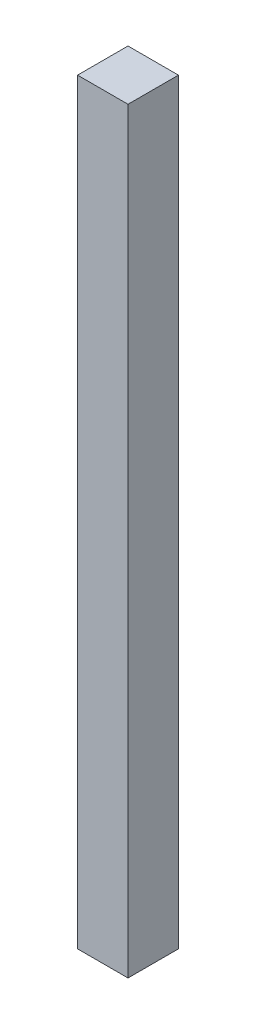
SolidWorks part; units mm, degrees
ref_plane "Plan de face" through (0, 0, 0) normal (0, 0, 1) x (1, 0, 0)
ref_plane "Plan de dessus" through (0, 0, 0) normal (0, 1, 0) x (1, 0, 0)
ref_plane "Plan de droite" through (0, 0, 0) normal (1, 0, 0) x (0, 0, -1)
sketch "Esquisse1" plane through (0, 0, 0) normal (0, 1, 0) x (1, 0, 0)
  line L1 (0, 0) -> (10, 0)
  line L2 (0, 0) -> (0, 10)
  line L3 (0, 10) -> (10, 10)
  line L4 (10, 0) -> (10, 10)
  dimension "D1" = 10
  dimension "D2" = 10
extrude "Boss.-Extru.1" add sketch "Esquisse1" along normal blind 150
